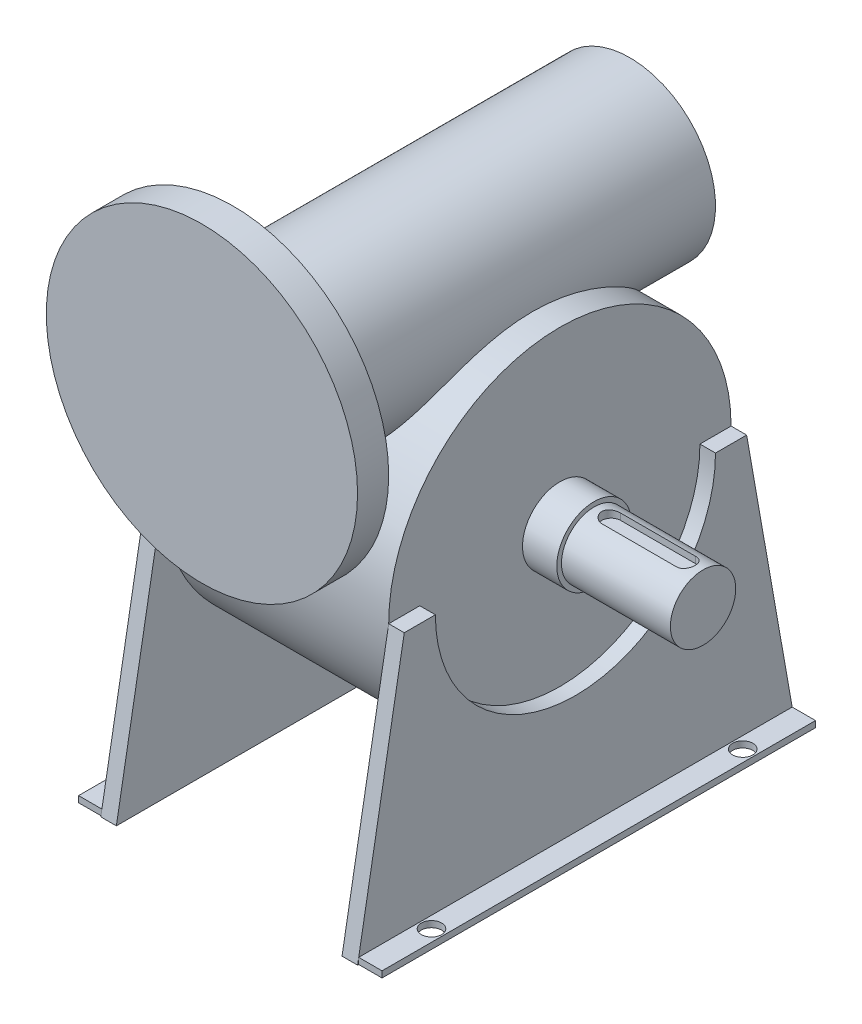
SolidWorks part; units mm, degrees
ref_plane "Front Plane" through (0, 0, 0) normal (0, 0, 1) x (1, 0, 0)
ref_plane "Top Plane" through (0, 0, 0) normal (0, 1, 0) x (1, 0, 0)
ref_plane "Right Plane" through (0, 0, 0) normal (1, 0, 0) x (0, 0, -1)
sketch "Sketch1" plane through (0, 0, 0) normal (0, 0, 1) x (1, 0, 0)
  circle A0 centre (0, 0) radius 100
  dimension "D1" = 200
extrude "Boss-Extrude1" add sketch "Sketch1" along normal blind 20
sketch "Sketch2" plane through (0, 0, 0) normal (0, 0, -1) x (-1, 0, 0)
  circle A0 centre (0, 0) radius 55
  dimension "D1" = 110
extrude "Boss-Extrude2" add sketch "Sketch2" along normal blind 255
sketch "Sketch3" plane through (0, 0, 0) normal (1, 0, 0) x (0, 0, -1)
  line L0 (255, -55) -> (255, 55) construction
  circle A0 centre (137.5, -110) radius 110
  dimension "D3" = 220
  dimension "D1" = 117.5
  dimension "D2" = 110
extrude "Boss-Extrude3" add sketch "Sketch3" along normal mid plane 145
sketch "Sketch4" plane through (72.5, 0, 0) normal (1, 0, 0) x (0, 0, -1)
  line L1 (-2.4756, -280) -> (137.5, -280)
  line L2 (137.5, -280) -> (137.5, -200)
  line L4 (-5.8842, -280.0208) -> (-2.4756, -280)
  line L5 (-2.4756, -280) -> (27.5, -110)
  line L7 (27.5, -110) -> (47.5, -110)
  circle A0 centre (137.5, -110) radius 110 construction
  arc A3 (47.5, -110) -> (137.5, -200) centre (137.5, -110) ccw
  circle M5 centre (137.5, -110) radius 110
  dimension "D1" = 170
  dimension "D2" = 90
  dimension "D3" = 10
  dimension "D4" = 0
extrude "Boss-Extrude4" add sketch "Sketch4" along normal blind 10 contours L5 L1 L2 M5 | A3 L7 L2 M5
mirror "Mirror1" about plane through (82.5, 0, -137.5) normal (0, 0, 1) of "Boss-Extrude4"
mirror "Mirror3" about plane through (0, 0, 0) normal (1, 0, 0) of "Boss-Extrude4"
mirror "Mirror4" about plane through (-82.5, 0, -137.5) normal (0, 0, -1) of "Mirror3"
sketch "Sketch5" plane through (72.5, 0, 0) normal (1, 0, 0) x (0, 0, -1)
  circle A0 centre (137.5, -110) radius 21
  arc A1 (247.5, -110) -> (27.5, -110) centre (137.5, -110) ccw construction
  dimension "D2" = 42
  dimension "D1" = 0
extrude "Boss-Extrude5" add sketch "Sketch5" along normal blind 92
sketch "Sketch7" plane through (72.5, 0, 0) normal (1, 0, 0) x (0, 0, -1)
  circle A0 centre (137.5, -110) radius 24
  dimension "D1" = 48
extrude "Boss-Extrude6" add sketch "Sketch7" along normal blind 22
ref_plane "Plane1" through (0, -89, 0) normal (0, 1, 0) x (1, 0, 0)
sketch "Sketch6" plane through (0, -89, 0) normal (0, 1, 0) x (1, 0, 0)
  line L0 (105.5, 143.5) -> (129.5, 143.5)
  line L1 (129.5, 143.5) -> (129.5, 131.5)
  line L2 (129.5, 131.5) -> (105.5, 131.5)
  line L3 (164.5, 158.5) -> (94.5, 158.5) construction
  line L5 (164.5, 116.5) -> (164.5, 158.5) construction
  arc A0 (105.5, 143.5) -> (105.5, 131.5) centre (105.5, 137.5) ccw
  dimension "D3" = 21
  dimension "D1" = 12
  dimension "D2" = 24
  dimension "D4" = 35
extrude "Cut-Extrude1" cut sketch "Sketch6" against normal blind 5
mirror "Mirror5" about plane through (129.5, -94, -143.5) normal (1, 0, 0) of "Cut-Extrude1"
sketch "Sketch8" plane through (82.5, 0, 0) normal (1, 0, 0) x (0, 0, -1)
  line L0 (-2.4756, -280) -> (27.5, -110) construction
  line L1 (-1.7703, -276) -> (276.7703, -276)
  line L2 (-1.7703, -276) -> (-1.7703, -280)
  line L3 (-1.7703, -280) -> (276.7703, -280)
  line L4 (276.7703, -276) -> (276.7703, -280)
  line L5 (-2.4756, -280) -> (277.4756, -280) construction
  line L6 (277.4756, -280) -> (247.5, -110) construction
  point P8 (0, 0)
  dimension "D1" = 4
extrude "Boss-Extrude7" add sketch "Sketch8" along normal blind 15
sketch "Sketch9" plane through (0, -280, 0) normal (0, -1, 0) x (1, 0, 0)
  line L2 (164.5, -137.5) -> (-132.8263, -137.5) construction
  line L3 (164.5, -158.5) -> (164.5, -116.5) construction
  point P0 (90, -37.5)
  point P1 (90, -237.5)
  point P3 (0, 0)
  dimension "D1" = 90
  dimension "D2" = 200
hole_wizard "Ø13.0 (13) Diameter Hole1" positions "Sketch12" profile "Sketch14" hole size "Ø13.0" standard "ISO" end condition through all
sketch "Sketch12" plane through (0, -280, 0) normal (0, -1, 0) x (-1, 0, 0)
  point P0 (-90, 37.5)
  point P4 (-90, 237.5)
sketch "Sketch14" plane through (90, -280, -37.5) normal (1, 0, 0) x (0, 0, -1)
  line L0 (0, 0) -> (0, 380)
  line L1 (0, 380) -> (6.5, 380)
  line L2 (6.5, 380) -> (6.5, 0)
  line L5 (6.5, 0) -> (0, 0)
  line L11 (0, -6.35) -> (0, 107.95) construction
  dimension "Thru Hole Dia." = 13
  dimension "Thru Hole Depth" = 380
mirror "Mirror8" about plane through (0, 0, 0) normal (1, 0, 0) of "Ø13.0 (13) Diameter Hole1", "Boss-Extrude7"
